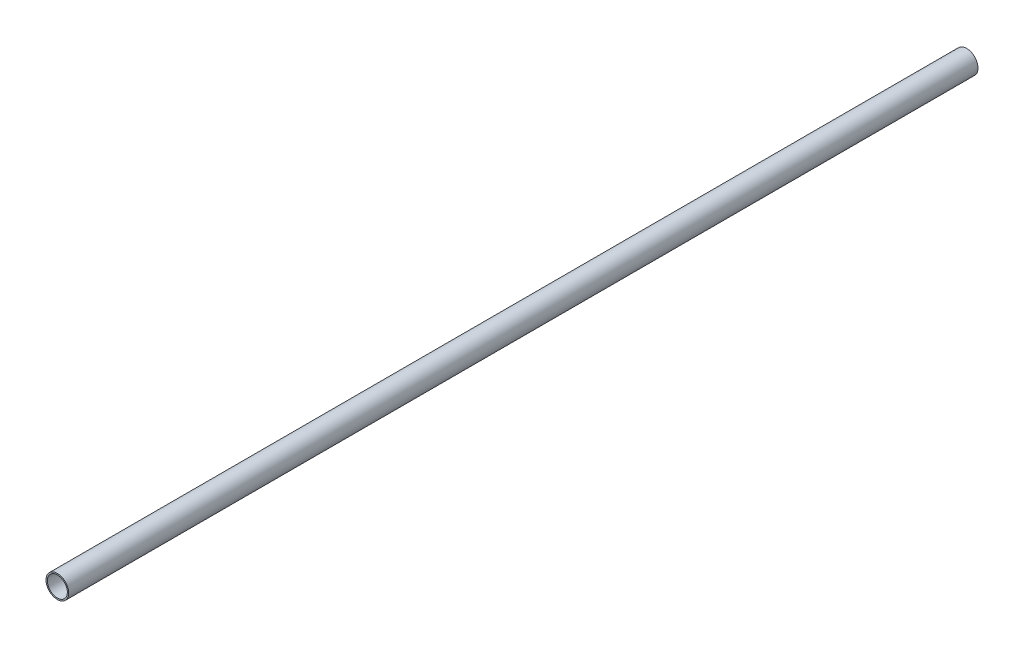
SolidWorks part; units mm, degrees
material "Carbon Fiber Tube - UD Approx"
ref_plane "Front Plane" through (0, 0, 0) normal (0, 0, 1) x (1, 0, 0)
ref_plane "Top Plane" through (0, 0, 0) normal (0, 1, 0) x (1, 0, 0)
ref_plane "Right Plane" through (0, 0, 0) normal (1, 0, 0) x (0, 0, -1)
sketch "Sketch1" plane through (0, 0, 0) normal (0, 0, 1) x (1, 0, 0)
  circle A0 centre (0, 0) radius 12.5
  circle A1 centre (0, 0) radius 11
  dimension "D1" = 25
  dimension "D2" = 22
extrude "Boss-Extrude1" add sketch "Sketch1" along normal blind 1000
